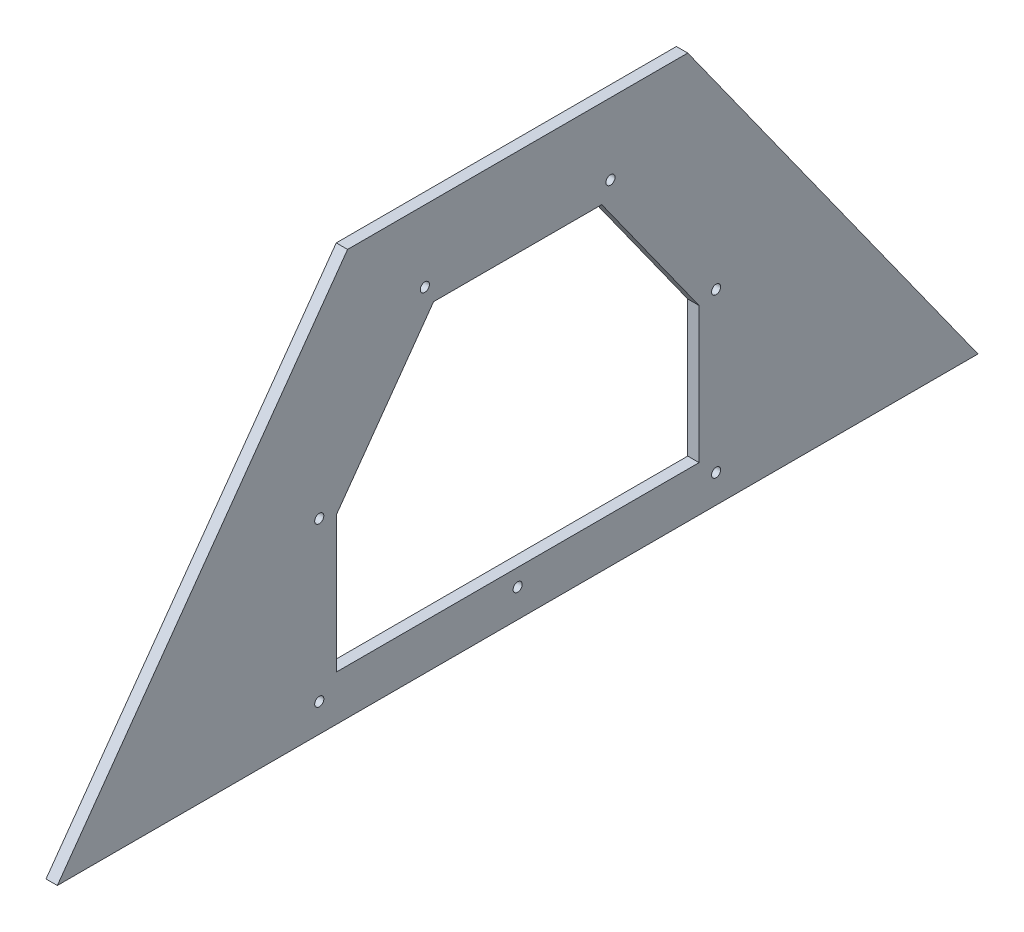
SolidWorks part; units mm, degrees
material "Pine"
ref_plane "Front Plane" through (0, 0, 0) normal (0, 0, 1) x (1, 0, 0)
ref_plane "Top Plane" through (0, 0, 0) normal (0, 1, 0) x (1, 0, 0)
ref_plane "Right Plane" through (0, 0, 0) normal (1, 0, 0) x (0, 0, -1)
sketch "Sketch1" plane through (0, 0, 0) normal (1, 0, 0) x (0, 0, -1)
  line L0 (257.81, 0) -> (-257.81, 0)
  line L2 (-257.81, 0) -> (-95.25, 227.2413)
  line L3 (-95.25, 227.2413) -> (95.25, 227.2413)
  line L4 (257.81, 0) -> (95.25, 227.2413)
  point P4 (0, 227.2413)
  point P5 (0, 0)
  dimension "D1" = 279.4
  dimension "D2" = 515.62
  dimension "D3" = 190.5
extrude "Boss-Extrude1" add sketch "Sketch1" along normal blind 6.35
sketch "Sketch3" plane through (6.35, 0, 0) normal (1, 0, 0) x (0, 0, -1)
  line L0 (-95.25, 227.2413) -> (-257.81, 0) construction
  line L1 (-47.0893, 177.8) -> (47.0893, 177.8)
  line L2 (-101.6, 101.6) -> (-101.6, 25.4)
  line L3 (-101.6, 25.4) -> (101.6, 25.4)
  line L4 (101.6, 101.6) -> (101.6, 25.4)
  line L5 (-257.81, 0) -> (257.81, 0) construction
  line L6 (-101.6, 101.6) -> (-47.0893, 177.8)
  line L7 (47.0893, 177.8) -> (101.6, 101.6)
  point P0 (0, 25.4)
  dimension "D1" = 203.2
  dimension "D2" = 25.4
  dimension "D3" = 76.2
  dimension "D5" = 152.4
extrude "Cut-Extrude1" cut sketch "Sketch3" against normal through all
hole_wizard "#10 Clearance Hole1" positions "Sketch4" profile "Sketch5" hole size "#10" standard "ANSI Inch" end condition through all
sketch "Sketch4" plane through (6.35, 0, 0) normal (1, 0, 0) x (0, 0, -1)
  line L29 (51.9868, 187.325) -> (-51.9868, 187.325)
  line L30 (111.125, 104.6562) -> (51.9868, 187.325)
  line L31 (111.125, 15.875) -> (111.125, 104.6562)
  line L32 (-111.125, 15.875) -> (111.125, 15.875)
  line L33 (-111.125, 104.6562) -> (-111.125, 15.875)
  line L34 (-51.9868, 187.325) -> (-111.125, 104.6562)
  line L35 (51.9868, 187.325) -> (-51.9868, 187.325)
  line L36 (111.125, 104.6562) -> (51.9868, 187.325)
  line L37 (111.125, 15.875) -> (111.125, 104.6562)
  line L38 (-111.125, 15.875) -> (111.125, 15.875)
  line L39 (-111.125, 104.6562) -> (-111.125, 15.875)
  line L40 (-51.9868, 187.325) -> (-111.125, 104.6562)
  point P119 (51.9868, 187.325)
  point P120 (-51.9868, 187.325)
  point P121 (111.125, 104.6562)
  point P122 (111.125, 15.875)
  point P123 (-111.125, 15.875)
  point P124 (-111.125, 104.6562)
  point P137 (0, 15.875)
  dimension "D1" = 9.525
sketch "Sketch5" plane through (6.35, 187.325, -51.9868) normal (0, 1, 0) x (0, 0, -1)
  line L0 (0, 0) -> (0, 6.35)
  line L1 (0, 6.35) -> (2.5527, 6.35)
  line L2 (2.5527, 6.35) -> (2.5527, 0)
  line L5 (2.5527, 0) -> (0, 0)
  line L11 (0, -6.35) -> (0, 107.95) construction
  dimension "Thru Hole Dia." = 5.1054
  dimension "Thru Hole Depth" = 6.35
sketch "Sketch6" plane through (6.35, 0, 0) normal (1, 0, 0) x (0, 0, -1)
  line L28 (120.65, 107.7123) -> (56.8842, 196.85)
  line L29 (120.65, 6.35) -> (120.65, 107.7123)
  line L30 (-120.65, 6.35) -> (120.65, 6.35)
  line L31 (-120.65, 107.7123) -> (-120.65, 6.35)
  line L32 (-56.8842, 196.85) -> (-120.65, 107.7123)
  line L33 (56.8842, 196.85) -> (-56.8842, 196.85)
  line L34 (120.65, 107.7123) -> (56.8842, 196.85) construction
  line L35 (120.65, 6.35) -> (120.65, 107.7123) construction
  line L36 (-120.65, 6.35) -> (120.65, 6.35) construction
  line L37 (-120.65, 107.7123) -> (-120.65, 6.35) construction
  line L38 (-56.8842, 196.85) -> (-120.65, 107.7123) construction
  line L39 (56.8842, 196.85) -> (-56.8842, 196.85) construction
  circle A0 centre (0, 57.15) radius 8.5423
  circle A1 centre (0, 15.875) radius 2.5527 construction
  dimension "D1" = 41.275
  dimension "D2" = 19.05
sketch "Sketch7" plane through (6.35, 0, 0) normal (1, 0, 0) x (0, 0, -1)
  line L0 (-142.9808, 139.7) -> (-131.9823, 133.35)
  line L1 (131.9823, 133.35) -> (142.9808, 139.7)
  arc A0 (-131.9823, 133.35) -> (131.9823, 133.35) centre (0, 57.15) cw
  arc A1 (-142.9808, 139.7) -> (142.9808, 139.7) centre (0, 57.15) cw
  point P7 (0, 209.55)
  dimension "D2" = 152.4
  dimension "D1" = 120
  dimension "D3" = 12.7
